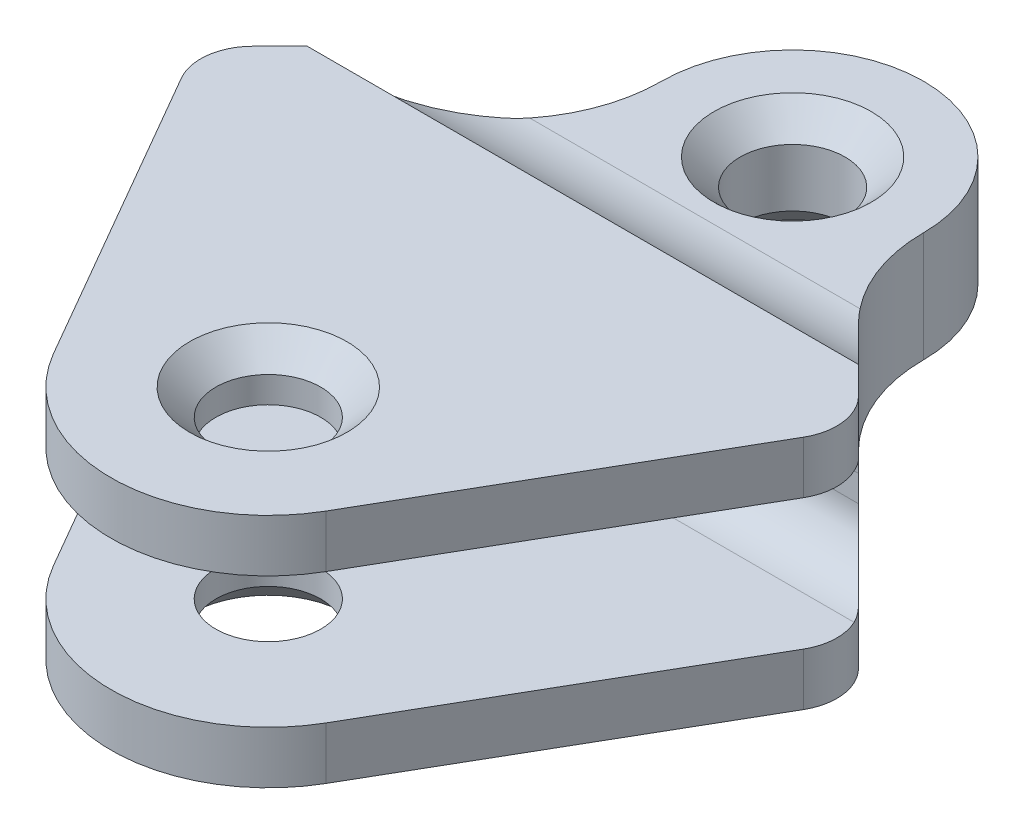
SolidWorks part; units mm, degrees
ref_plane "Front Plane" through (0, 0, 0) normal (0, 0, 1) x (1, 0, 0)
ref_plane "Top Plane" through (0, 0, 0) normal (0, 1, 0) x (1, 0, 0)
ref_plane "Right Plane" through (0, 0, 0) normal (1, 0, 0) x (0, 0, -1)
sketch "Sketch1" plane through (0, 0, 0) normal (0, 1, 0) x (1, 0, 0)
  line L0 (0, 0) -> (0, -37.6627) construction
  line L1 (0, -37.6627) -> (0, 0) construction
  line L2 (0, 0) -> (0, 126.3331) construction
  line L3 (-25.9808, -15) -> (-59.3297, 42.762)
  line L4 (25.9808, -15) -> (59.3297, 42.762)
  line L5 (-33.7868, 78.7868) -> (-57.7405, 54.8331)
  line L6 (33.7868, 78.7868) -> (57.7405, 54.8331)
  circle A0 centre (0, 100) radius 10
  circle A1 centre (0, 0) radius 10
  arc A2 (-25.9808, -15) -> (25.9808, -15) centre (0, 0) ccw
  arc A3 (25, 100) -> (-25, 100) centre (0, 100) ccw
  arc A4 (-33.7868, 78.7868) -> (-25, 100) centre (-55, 100) ccw
  arc A5 (33.7868, 78.7868) -> (25, 100) centre (55, 100) cw
  arc A6 (57.7405, 54.8331) -> (59.3297, 42.762) centre (50.6694, 47.762) cw
  arc A7 (-57.7405, 54.8331) -> (-59.3297, 42.762) centre (-50.6694, 47.762) ccw
  point P11 (0, 0)
  point P17 (-38.1248, 99.1817)
  point P18 (-55, 100)
  point P24 (63.1663, 49.4073)
  point P27 (-63.1663, 49.4073)
  dimension "D1" = 20
  dimension "D2" = 20
  dimension "D4" = 20
  dimension "D5" = 50
  dimension "D6" = 60
  dimension "D8" = 30
  dimension "D9" = 10
  dimension "D3" = 100
  dimension "D7" = 90
extrude "Boss-Extrude1" add sketch "Sketch1" along normal mid plane 45
sketch "Sketch2" plane through (0, 0, 0) normal (1, 0, 0) x (0, 0, -1)
  line L0 (-30, 22.5) -> (-30, -22.5) construction
  line L1 (-30, 12.5) -> (52, 12.5)
  line L2 (-30, 12.5) -> (-30, -12.5)
  line L3 (-30, -12.5) -> (52, -12.5)
  line L4 (62, 2.5) -> (62, -2.5)
  line L5 (0, 0) -> (30.342, 0) construction
  line L6 (125, 0) -> (78.7868, 0) construction
  line L7 (125, -22.5) -> (125, 22.5) construction
  line L8 (78.7868, 22.5) -> (78.7868, -22.5) construction
  line L9 (81.3542, 10.5) -> (125, 10.5)
  line L10 (125, 22.5) -> (100, 22.5) construction
  line L11 (54.8331, 22.5) -> (78.7868, 22.5) construction
  line L12 (60, 22.5) -> (78.7868, 22.5)
  line L13 (78.7868, 22.5) -> (125, 22.5)
  line L14 (125, 22.5) -> (125, 10.5)
  line L15 (125, -22.5) -> (125, -10.5)
  line L16 (78.7868, -22.5) -> (125, -22.5)
  line L17 (60, -22.5) -> (78.7868, -22.5)
  line L18 (81.3542, -10.5) -> (125, -10.5)
  arc A0 (52, -12.5) -> (62, -2.5) centre (52, -2.5) ccw
  arc A1 (52, 12.5) -> (62, 2.5) centre (52, 2.5) cw
  arc A2 (60, 22.5) -> (81.3542, 10.5) centre (81.3542, 35.5) ccw
  arc A3 (60, -22.5) -> (81.3542, -10.5) centre (81.3542, -35.5) cw
  point P13 (62, 12.5)
  dimension "D3" = 10
  dimension "D4" = 25
  dimension "D1" = 25
  dimension "D2" = 92
  dimension "D5" = 12
  dimension "D6" = 65
extrude "Cut-Extrude1" cut sketch "Sketch2" against normal through all both and the other way through all
chamfer "Chamfer1" distance 5 angle 45 4 edges at (0, 10.5, -110) (0, -10.5, -90) (0, 22.5, 10) (0, -22.5, 10)
